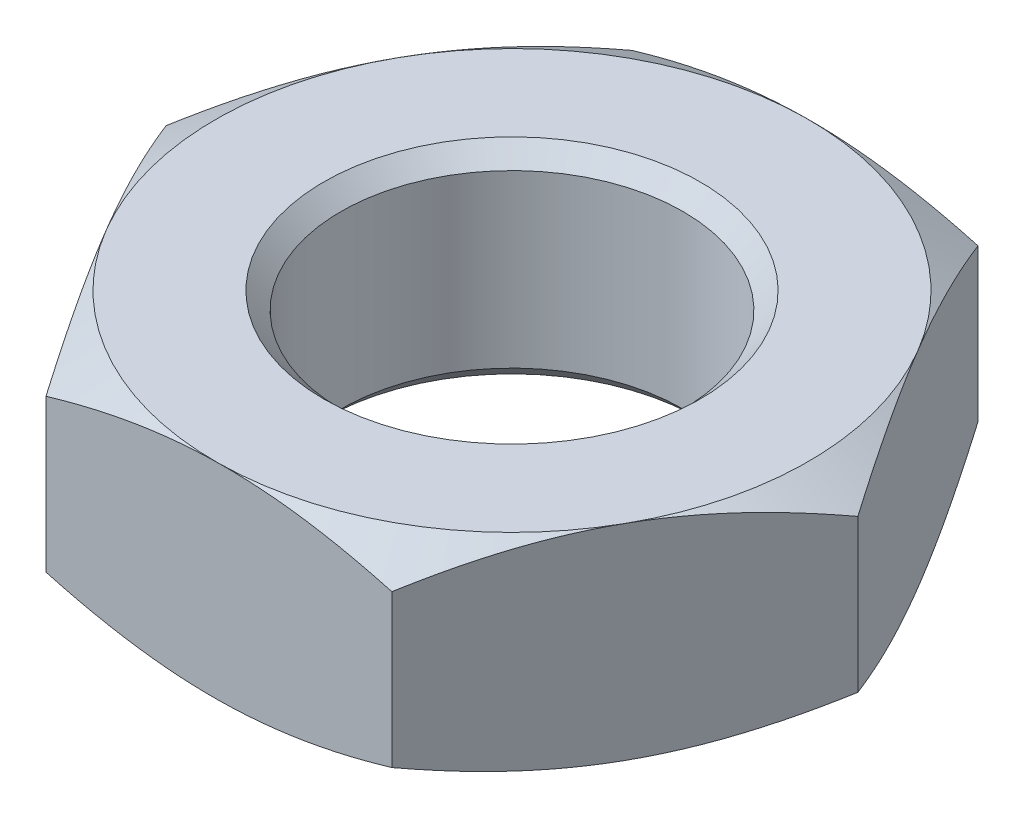
SolidWorks part; units mm, degrees
ref_plane "Front Plane" through (0, 0, 0) normal (0, 0, 1) x (1, 0, 0)
ref_plane "Top Plane" through (0, 0, 0) normal (0, 1, 0) x (1, 0, 0)
ref_plane "Right Plane" through (0, 0, 0) normal (1, 0, 0) x (0, 0, -1)
sketch "Sketch1" plane through (0, 0, 0) normal (0, 1, 0) x (1, 0, 0)
  line L1 (-4.9057, -8.7147) -> (5.0943, -8.6058)
  line L2 (5.0943, -8.6058) -> (10, 0.1088)
  line L3 (10, 0.1088) -> (4.9057, 8.7147)
  line L4 (4.9057, 8.7147) -> (-5.0943, 8.6058)
  line L5 (-5.0943, 8.6058) -> (-10, -0.1088)
  line L6 (-10, -0.1088) -> (-4.9057, -8.7147)
  circle A0 centre (0, 0) radius 8.6608 construction
  circle A1 centre (0, 0) radius 5
  dimension "D1" = 20
extrude "Boss-Extrude1" add sketch "Sketch1" along normal mid plane 6
chamfer "Chamfer1" distance 0.5 angle 45 2 edges at (0, -3, 5) (0, 3, 5)
sketch "Sketch2" plane through (0, 3, 0) normal (0, 1, 0) x (1, 0, 0)
  circle A0 centre (0, 0) radius 8.6608
extrude "Cut-Extrude1" cut sketch "Sketch2" against normal blind 10 draft 60 flip side to cut
mirror "Mirror1" about plane through (0, 0, 0) normal (0, 1, 0) of "Cut-Extrude1"
